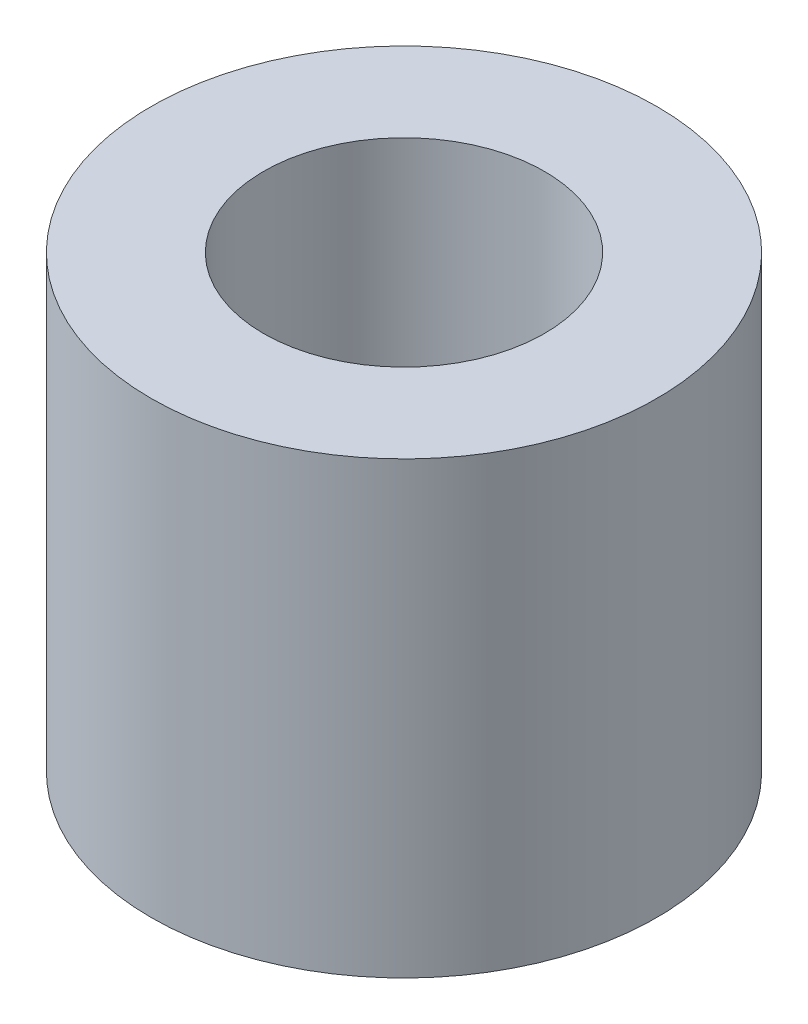
SolidWorks part; units mm, degrees
ref_plane "Front Plane" through (0, 0, 0) normal (0, 0, 1) x (1, 0, 0)
ref_plane "Top Plane" through (0, 0, 0) normal (0, 1, 0) x (1, 0, 0)
ref_plane "Right Plane" through (0, 0, 0) normal (1, 0, 0) x (0, 0, -1)
sketch "Sketch1" plane through (0, 0, 0) normal (0, 1, 0) x (1, 0, 0)
  circle A0 centre (0, 0) radius 3.175
  circle A1 centre (0, 0) radius 5.715
  dimension "D1" = 6.35
  dimension "D2" = 2.54
extrude "Boss-Extrude1" add sketch "Sketch1" along normal blind 10.16
